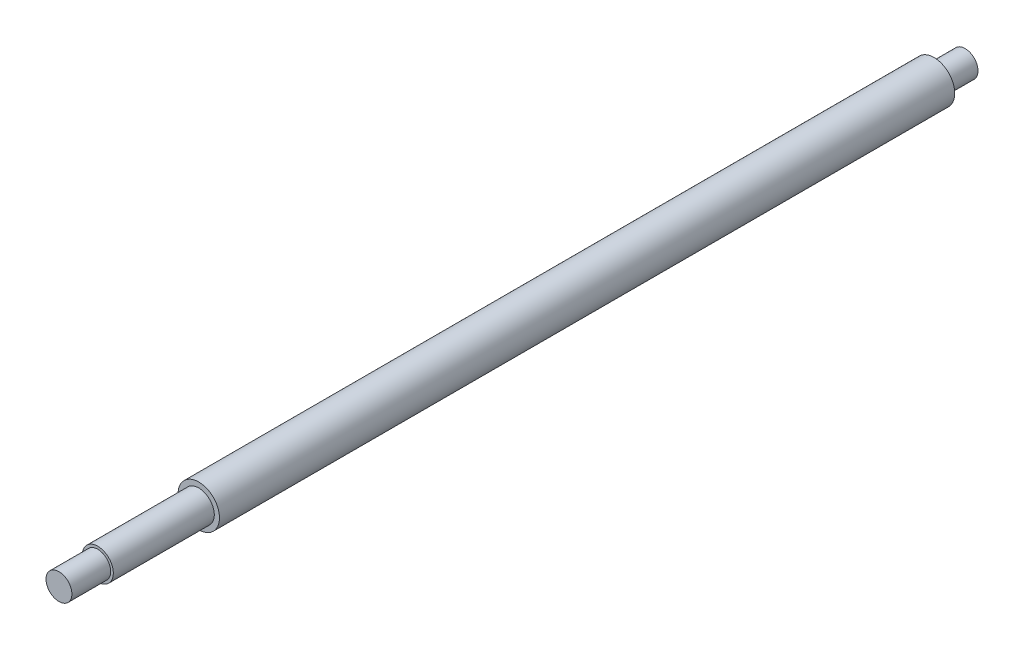
SolidWorks part; units mm, degrees
material "1060 Alloy"
ref_plane "Front Plane" through (0, 0, 0) normal (0, 0, 1) x (1, 0, 0)
ref_plane "Top Plane" through (0, 0, 0) normal (0, 1, 0) x (1, 0, 0)
ref_plane "Right Plane" through (0, 0, 0) normal (1, 0, 0) x (0, 0, -1)
sketch "Sketch1" plane through (0, 0, 0) normal (1, 0, 0) x (0, 0, -1)
  line L0 (0, 0) -> (-42.623, 0) construction
  line L1 (-338.68, 0) -> (-338.68, 5)
  line L2 (-338.68, 5) -> (-323.68, 5)
  line L3 (-323.68, 5) -> (-323.68, 6)
  line L4 (-323.68, 6) -> (-284.68, 6)
  line L5 (-284.68, 6) -> (-284.68, 8)
  line L6 (-284.68, 8) -> (-0.68, 8)
  line L7 (-0.68, 8) -> (-0.68, 5)
  line L8 (-0.68, 5) -> (11.32, 5)
  line L9 (11.32, 5) -> (11.32, 0)
  line L10 (-338.68, 0) -> (11.32, 0)
  line L12 (-6.68, 0) -> (-6.68, -14) construction
  point P2 (-139.727, -14)
  point P16 (-6.68, 0)
  dimension "D1" = 5
  dimension "D2" = 6
  dimension "D3" = 8
  dimension "D4" = 5
  dimension "D5" = 12
  dimension "D6" = 39
  dimension "D7" = 15
  dimension "D8" = 18
  dimension "D9" = 133.7816
  dimension "D10" = 350
revolve "Revolve1" add sketch "Sketch1" angle 360 about L0
sketch "Sketch3" [suppressed] plane through (0, 0, 0) normal (1, 0, 0) x (0, 0, -1)
  line L0 (-80.9254, 0) -> (-123.5483, 0) construction
  line L1 (-275.75, 0) -> (-275.75, 5)
  line L2 (-275.75, 5) -> (-260.75, 5)
  line L3 (-260.75, 5) -> (-260.75, 6)
  line L4 (-260.75, 6) -> (-221.75, 6)
  line L5 (-221.75, 6) -> (-221.75, 8)
  line L6 (-221.75, 8) -> (-12, 8)
  line L7 (-12, 8) -> (-12, 5)
  line L8 (-12, 5) -> (0, 5)
  line L9 (0, 5) -> (0, 0)
  line L10 (-275.75, 0) -> (0, 0)
  dimension "D1" = 10
  dimension "D2" = 6
  dimension "D3" = 8
  dimension "D4" = 10
  dimension "D5" = 15
  dimension "D6" = 39
  dimension "D7" = 209.75
  dimension "D8" = 12
revolve "Revolve2" [suppressed] add sketch "Sketch3" angle 360 about L0
